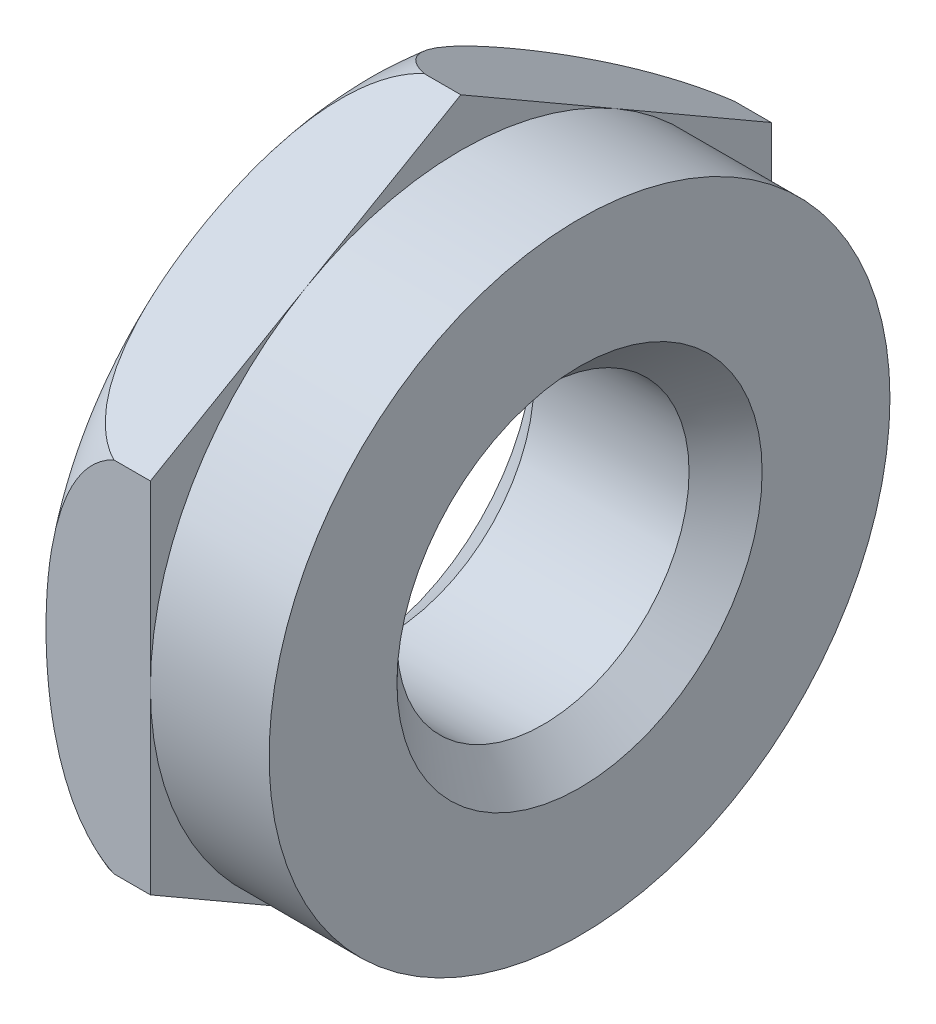
SolidWorks part; units mm, degrees
ref_plane "Plan de face" through (0, 0, 0) normal (0, 0, 1) x (1, 0, 0)
ref_plane "Plan de dessus" through (0, 0, 0) normal (0, 1, 0) x (1, 0, 0)
ref_plane "Plan de droite" through (0, 0, 0) normal (1, 0, 0) x (0, 0, -1)
sketch "Esquisse2" plane through (0, 0, 0) normal (1, 0, 0) x (0, 0, -1)
  line L1 (0, 9.815) -> (-8.5, 4.9075)
  line L2 (-8.5, 4.9075) -> (-8.5, -4.9075)
  line L3 (-8.5, -4.9075) -> (0, -9.815)
  line L4 (0, -9.815) -> (8.5, -4.9075)
  line L5 (8.5, -4.9075) -> (8.5, 4.9075)
  line L6 (8.5, 4.9075) -> (0, 9.815)
  circle A0 centre (0, 0) radius 8.5 construction
  circle A1 centre (0, 0) radius 4
  dimension "D2" = 8
  dimension "D1" = 17
extrude "Extrusion1" add sketch "Esquisse2" along normal blind 3.25 and the other way blind 3
sketch "Esquisse3" plane through (0, 0, 0) normal (1, 0, 0) x (0, 0, -1)
  line L0 (8.5, 4.9075) -> (0, 9.815) construction
  circle A0 centre (0, 0) radius 8.5
extrude "Enlèv. mat.-Extru.1" cut sketch "Esquisse3" along normal through all flip side to cut
sketch "Esquisse4" plane through (0, 0, 0) normal (0, 0, 1) x (1, 0, 0)
  line L0 (0, 0) -> (-7.2896, 0) construction
  line L1 (-1, 9.815) -> (-3, 9.815)
  line L2 (0, 9.815) -> (-3, 9.815) construction
  line L4 (-3, 9.815) -> (-3, 8.25)
  line L5 (-3, 9.815) -> (-3, 4.9075) construction
  arc A0 (-3, 8.25) -> (-1, 9.815) centre (-0.325, 6.8919) cw
  dimension "D3" = 3
  dimension "D1" = 2
  dimension "D2" = 16.5
revolve "Enlèvement de matière-Révolution1" cut sketch "Esquisse4" angle 360 about L0
chamfer "Chanfrein1" distance 1 angle 45 2 edges at (3.25, 0, -4) (-3, 0, -4)
